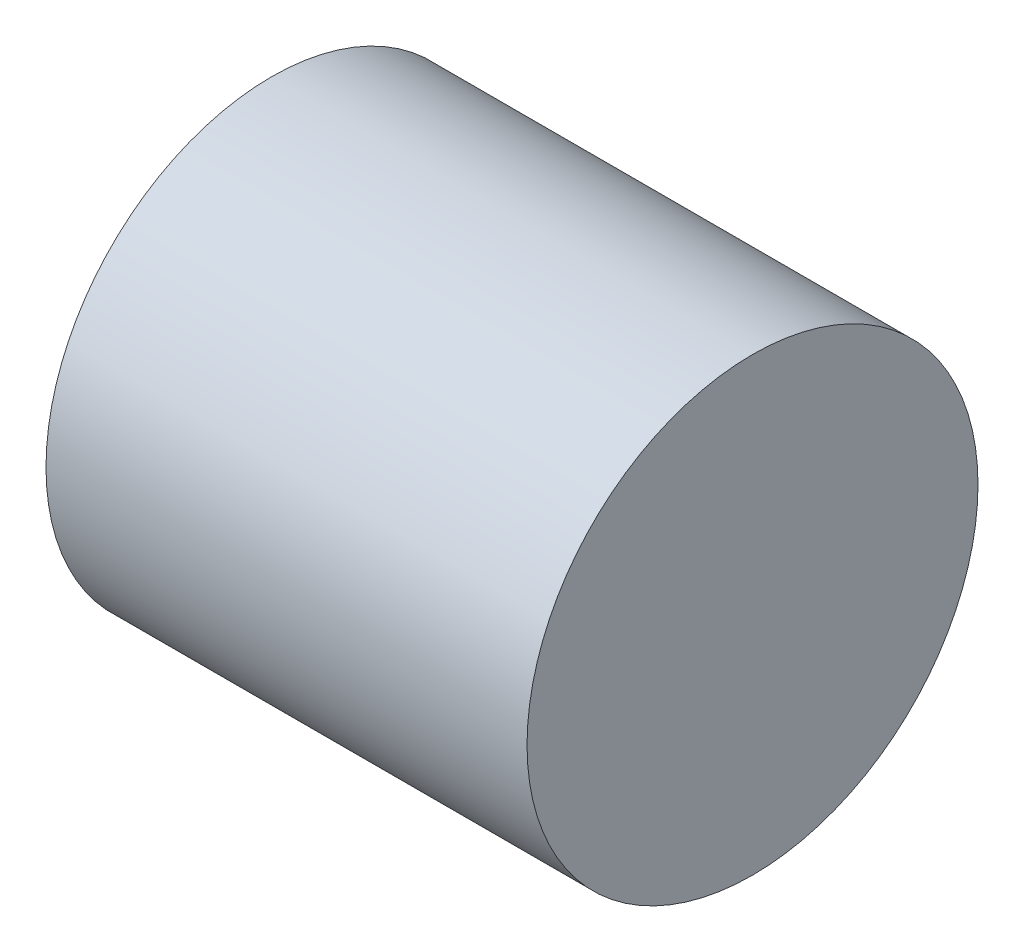
SolidWorks part; units mm, degrees
ref_plane "Front Plane" through (0, 0, 0) normal (0, 0, 1) x (1, 0, 0)
ref_plane "Top Plane" through (0, 0, 0) normal (0, 1, 0) x (1, 0, 0)
ref_plane "Right Plane" through (0, 0, 0) normal (1, 0, 0) x (0, 0, -1)
sketch "Sketch1" plane through (0, 0, 0) normal (0, 0, 1) x (1, 0, 0)
  line L0 (-19.537, 0) -> (23.5185, 0) construction
  line L1 (17.6852, 0) -> (17.6852, 15)
  line L2 (17.6852, 15) -> (-14.3148, 15)
  line L3 (-14.3148, 15) -> (-14.3148, 1)
  line L4 (-14.3148, 1) -> (-12.3148, 1)
  line L5 (-12.3148, 1) -> (-12.3148, 0)
  line L6 (17.6852, 0) -> (-12.3148, 0)
  dimension "D1" = 15
  dimension "D2" = 32
  dimension "D3" = 2
  dimension "D4" = 1
revolve "Revolve1" add sketch "Sketch1" angle 360 about L0
